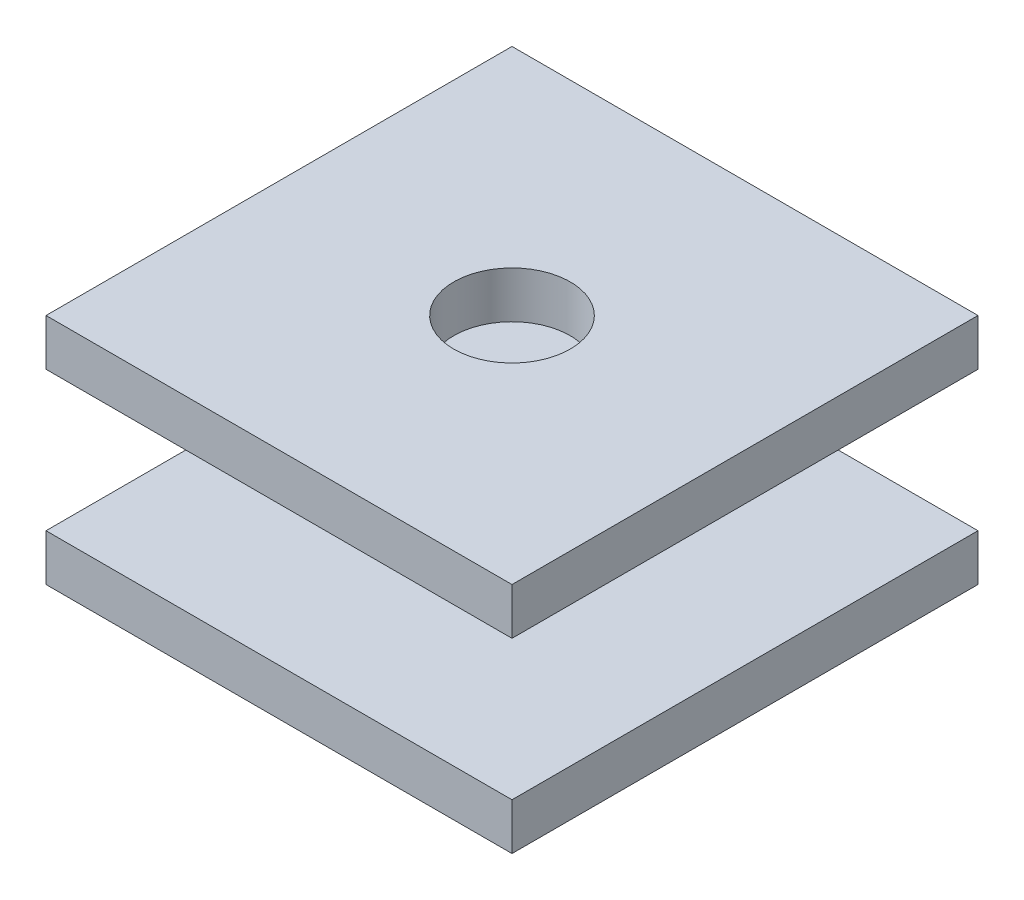
SolidWorks part; units mm, degrees
ref_plane "Front Plane" through (0, 0, 0) normal (0, 0, 1) x (1, 0, 0)
ref_plane "Top Plane" through (0, 0, 0) normal (0, 1, 0) x (1, 0, 0)
ref_plane "Right Plane" through (0, 0, 0) normal (1, 0, 0) x (0, 0, -1)
sketch "Sketch1" plane through (0, 0, 0) normal (0, 1, 0) x (1, 0, 0)
  line L1 (0, 0) -> (25.4, 0)
  line L2 (0, 0) -> (0, 25.4)
  line L3 (0, 25.4) -> (25.4, 25.4)
  line L4 (25.4, 0) -> (25.4, 25.4)
  dimension "D1" = 25.4
  dimension "D2" = 25.4
extrude "Boss-Extrude1" add sketch "Sketch1" along normal blind 2.54
sketch "Sketch2" plane through (0, 0, 0) normal (0, -1, 0) x (1, 0, 0)
  line L0 (0, -12.7) -> (25.4, -12.7) construction
  line L1 (0, -25.4) -> (0, 0) construction
  line L2 (25.4, 0) -> (25.4, -25.4) construction
  circle A0 centre (12.7, -12.7) radius 2.54
  dimension "D1" = 5.08
extrude "Boss-Extrude2" add sketch "Sketch2" along normal blind 2.54
sketch "Sketch3" plane through (0, 2.54, 0) normal (0, 1, 0) x (1, 0, 0)
  line L0 (0, 12.7) -> (25.4, 12.7) construction
  line L1 (0, 25.4) -> (0, 0) construction
  line L2 (25.4, 0) -> (25.4, 25.4) construction
  circle A0 centre (12.7, 12.7) radius 3.81
  dimension "D1" = 7.62
extrude "Boss-Extrude3" add sketch "Sketch3" along normal blind 7.62
sketch "Sketch4" plane through (0, 10.16, 0) normal (0, 1, 0) x (1, 0, 0)
  line L1 (0, 0) -> (25.4, 0)
  line L2 (0, 0) -> (0, 25.4)
  line L3 (0, 25.4) -> (25.4, 25.4)
  line L4 (25.4, 0) -> (25.4, 25.4)
  line L5 (0, 0) -> (25.4, 25.4) construction
  line L6 (0, 25.4) -> (25.4, 0) construction
  point P0 (12.7, 12.7)
extrude "Boss-Extrude4" add sketch "Sketch4" along normal blind 2.54
sketch "Sketch5" plane through (0, 12.7, 0) normal (0, 1, 0) x (1, 0, 0)
  line L0 (0, 12.7) -> (25.4, 12.7) construction
  line L1 (0, 25.4) -> (0, 0) construction
  line L2 (25.4, 0) -> (25.4, 25.4) construction
  circle A0 centre (12.7, 12.7) radius 3.175
  dimension "D1" = 6.35
extrude "Cut-Extrude2" cut sketch "Sketch5" against normal blind 2.54
